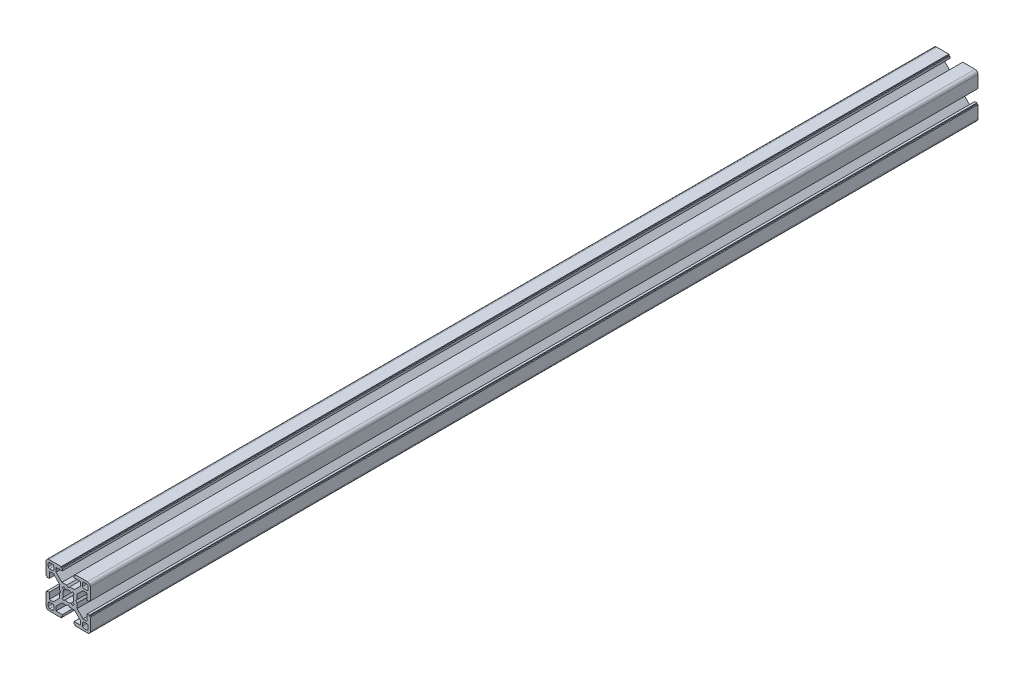
SolidWorks part; units mm, degrees
material "6063-O, Barra estrusa (SS)"
ref_plane "Piano frontale" through (0, 0, 0) normal (0, 0, 1) x (1, 0, 0)
ref_plane "Piano superiore" through (0, 0, 0) normal (0, 1, 0) x (1, 0, 0)
ref_plane "Piano destro" through (0, 0, 0) normal (1, 0, 0) x (0, 0, -1)
sketch "Schizzo1" plane through (0, 0, 0) normal (0, 0, 1) x (1, 0, 0)
  line L0 (-125.0647, 0) -> (53.776, 0) construction
  line L1 (0, -44.8297) -> (0, 95.2781) construction
  line L2 (-15, 13) -> (-15, 4.7)
  line L3 (-15, 4.7) -> (-14.3, 4.7)
  line L4 (-14.3, 4.7) -> (-14.3, 4)
  line L5 (-14.3, 4) -> (-12.8, 4)
  line L6 (-12.8, 4) -> (-12.8, 8.25)
  line L7 (-12.8, 8.25) -> (-10.0178, 8.25)
  line L8 (-10.0178, 8.25) -> (-6, 4.2322)
  line L9 (-6, 4.2322) -> (-6, 1)
  line L10 (-6, 1) -> (-5, 0)
  line L11 (-1, 6) -> (0, 5)
  line L12 (0, 0) -> (-161.3113, 161.3113) construction
  line L13 (-4.2322, 6) -> (-1, 6)
  line L14 (-8.25, 10.0178) -> (-4.2322, 6)
  line L15 (-8.25, 12.8) -> (-8.25, 10.0178)
  line L16 (-4, 12.8) -> (-8.25, 12.8)
  line L17 (-4, 14.3) -> (-4, 12.8)
  line L18 (-4.7, 14.3) -> (-4, 14.3)
  line L19 (-4.7, 15) -> (-4.7, 14.3)
  line L20 (-13, 15) -> (-4.7, 15)
  line L21 (13.5, 10.75) -> (13.5, 12.5)
  line L22 (10.75, 13.5) -> (12.5, 13.5)
  line L23 (9.75, 10.75) -> (9.75, 12.5)
  line L24 (10.75, 9.75) -> (12.5, 9.75)
  line L25 (10.75, -13.5) -> (12.5, -13.5)
  line L26 (13.5, -10.75) -> (13.5, -12.5)
  line L27 (10.75, -9.75) -> (12.5, -9.75)
  line L28 (9.75, -10.75) -> (9.75, -12.5)
  line L29 (-13.5, -10.75) -> (-13.5, -12.5)
  line L30 (-10.75, -13.5) -> (-12.5, -13.5)
  line L31 (-9.75, -10.75) -> (-9.75, -12.5)
  line L32 (-10.75, -9.75) -> (-12.5, -9.75)
  line L33 (1.9955, 3.0562) -> (3.0052, 4.0659)
  line L34 (3.0052, 4.0659) -> (4.0659, 3.0052)
  line L35 (4.0659, 3.0052) -> (3.0562, 1.9955)
  line L36 (3.0562, -1.9955) -> (4.0659, -3.0052)
  line L37 (4.0659, -3.0052) -> (3.0052, -4.0659)
  line L38 (3.0052, -4.0659) -> (1.9955, -3.0562)
  line L39 (-1.9955, -3.0562) -> (-3.0052, -4.0659)
  line L40 (-3.0052, -4.0659) -> (-4.0659, -3.0052)
  line L41 (-4.0659, -3.0052) -> (-3.0562, -1.9955)
  line L42 (1, 6) -> (0, 5)
  line L43 (4.2322, 6) -> (1, 6)
  line L44 (8.25, 10.0178) -> (4.2322, 6)
  line L45 (8.25, 12.8) -> (8.25, 10.0178)
  line L46 (4, 12.8) -> (8.25, 12.8)
  line L47 (12.8, 4) -> (12.8, 8.25)
  line L48 (12.8, 8.25) -> (10.0178, 8.25)
  line L49 (10.0178, 8.25) -> (6, 4.2322)
  line L50 (6, 4.2322) -> (6, 1)
  line L51 (6, 1) -> (5, 0)
  line L52 (6, -1) -> (5, 0)
  line L53 (6, -4.2322) -> (6, -1)
  line L54 (10.0178, -8.25) -> (6, -4.2322)
  line L55 (12.8, -8.25) -> (10.0178, -8.25)
  line L56 (12.8, -4) -> (12.8, -8.25)
  line L57 (4, -12.8) -> (8.25, -12.8)
  line L58 (8.25, -12.8) -> (8.25, -10.0178)
  line L59 (8.25, -10.0178) -> (4.2322, -6)
  line L60 (4.2322, -6) -> (1, -6)
  line L61 (1, -6) -> (0, -5)
  line L62 (-1, -6) -> (0, -5)
  line L63 (-4.2322, -6) -> (-1, -6)
  line L64 (-8.25, -10.0178) -> (-4.2322, -6)
  line L65 (-8.25, -12.8) -> (-8.25, -10.0178)
  line L66 (-4, -12.8) -> (-8.25, -12.8)
  line L67 (-12.8, -4) -> (-12.8, -8.25)
  line L68 (-12.8, -8.25) -> (-10.0178, -8.25)
  line L69 (-10.0178, -8.25) -> (-6, -4.2322)
  line L70 (-6, -4.2322) -> (-6, -1)
  line L71 (-6, -1) -> (-5, 0)
  line L72 (4, 14.3) -> (4, 12.8)
  line L73 (4.7, 14.3) -> (4, 14.3)
  line L74 (4.7, 15) -> (4.7, 14.3)
  line L75 (-3.0562, 1.9955) -> (-4.0659, 3.0052)
  line L76 (-4.0659, 3.0052) -> (-3.0052, 4.0659)
  line L77 (-3.0052, 4.0659) -> (-1.9955, 3.0562)
  line L78 (15, 4.7) -> (14.3, 4.7)
  line L79 (-10.75, 9.75) -> (-12.5, 9.75)
  line L80 (-9.75, 10.75) -> (-9.75, 12.5)
  line L81 (-10.75, 13.5) -> (-12.5, 13.5)
  line L82 (-13.5, 10.75) -> (-13.5, 12.5)
  line L83 (14.3, 4.7) -> (14.3, 4)
  line L84 (14.3, 4) -> (12.8, 4)
  line L85 (14.3, -4) -> (12.8, -4)
  line L86 (14.3, -4.7) -> (14.3, -4)
  line L87 (15, -4.7) -> (14.3, -4.7)
  line L88 (4.7, -15) -> (4.7, -14.3)
  line L89 (4.7, -14.3) -> (4, -14.3)
  line L90 (4, -14.3) -> (4, -12.8)
  line L91 (-4, -14.3) -> (-4, -12.8)
  line L92 (-4.7, -14.3) -> (-4, -14.3)
  line L93 (-4.7, -15) -> (-4.7, -14.3)
  line L94 (-15, -4.7) -> (-14.3, -4.7)
  line L95 (-14.3, -4.7) -> (-14.3, -4)
  line L96 (-14.3, -4) -> (-12.8, -4)
  line L97 (4, 14.3) -> (4, 12.8)
  line L98 (4.7, 14.3) -> (4, 14.3)
  line L99 (4.7, 15) -> (4.7, 14.3)
  line L100 (15, 4.7) -> (14.3, 4.7)
  line L101 (14.3, 4.7) -> (14.3, 4)
  line L102 (14.3, 4) -> (12.8, 4)
  line L103 (13, 15) -> (4.7, 15)
  line L104 (15, 13) -> (15, 4.7)
  line L105 (14.3, -4) -> (12.8, -4)
  line L106 (14.3, -4.7) -> (14.3, -4)
  line L107 (15, -4.7) -> (14.3, -4.7)
  line L108 (4.7, -15) -> (4.7, -14.3)
  line L109 (4.7, -14.3) -> (4, -14.3)
  line L110 (4, -14.3) -> (4, -12.8)
  line L111 (15, -13) -> (15, -4.7)
  line L112 (13, -15) -> (4.7, -15)
  line L113 (-4, -14.3) -> (-4, -12.8)
  line L114 (-4.7, -14.3) -> (-4, -14.3)
  line L115 (-4.7, -15) -> (-4.7, -14.3)
  line L116 (-15, -4.7) -> (-14.3, -4.7)
  line L117 (-14.3, -4.7) -> (-14.3, -4)
  line L118 (-14.3, -4) -> (-12.8, -4)
  line L119 (-13, -15) -> (-4.7, -15)
  line L120 (-15, -13) -> (-15, -4.7)
  arc A0 (-3.65, 0) -> (-3.0562, 1.9955) centre (0, 0) cw
  arc A1 (-1.9955, 3.0562) -> (0, 3.65) centre (0, 0) cw
  arc A2 (-13, 15) -> (-15, 13) centre (-13, 13) ccw
  arc A3 (-13.5, 10.75) -> (-12.5, 9.75) centre (-12.5, 10.75) ccw
  arc A4 (-9.75, 10.75) -> (-10.75, 9.75) centre (-10.75, 10.75) cw
  arc A5 (-10.75, 13.5) -> (-9.75, 12.5) centre (-10.75, 12.5) cw
  arc A6 (-12.5, 13.5) -> (-13.5, 12.5) centre (-12.5, 12.5) ccw
  arc A7 (13.5, 12.5) -> (12.5, 13.5) centre (12.5, 12.5) ccw
  arc A8 (13.5, 10.75) -> (12.5, 9.75) centre (12.5, 10.75) cw
  arc A9 (10.75, 9.75) -> (9.75, 10.75) centre (10.75, 10.75) cw
  arc A10 (10.75, 13.5) -> (9.75, 12.5) centre (10.75, 12.5) ccw
  arc A11 (12.5, -13.5) -> (13.5, -12.5) centre (12.5, -12.5) ccw
  arc A12 (10.75, -13.5) -> (9.75, -12.5) centre (10.75, -12.5) cw
  arc A13 (9.75, -10.75) -> (10.75, -9.75) centre (10.75, -10.75) cw
  arc A14 (13.5, -10.75) -> (12.5, -9.75) centre (12.5, -10.75) ccw
  arc A15 (-13.5, -12.5) -> (-12.5, -13.5) centre (-12.5, -12.5) ccw
  arc A16 (-13.5, -10.75) -> (-12.5, -9.75) centre (-12.5, -10.75) cw
  arc A17 (-10.75, -9.75) -> (-9.75, -10.75) centre (-10.75, -10.75) cw
  arc A18 (-10.75, -13.5) -> (-9.75, -12.5) centre (-10.75, -12.5) ccw
  arc A19 (0, 3.65) -> (1.9955, 3.0562) centre (0, 0) cw
  arc A20 (3.0562, 1.9955) -> (3.65, 0) centre (0, 0) cw
  arc A21 (3.65, 0) -> (3.0562, -1.9955) centre (0, 0) cw
  arc A22 (1.9955, -3.0562) -> (0, -3.65) centre (0, 0) cw
  arc A23 (0, -3.65) -> (-1.9955, -3.0562) centre (0, 0) cw
  arc A24 (-3.0562, -1.9955) -> (-3.65, 0) centre (0, 0) cw
  arc A25 (15, 13) -> (13, 15) centre (13, 13) ccw
  arc A26 (13, -15) -> (15, -13) centre (13, -13) ccw
  arc A27 (-15, -13) -> (-13, -15) centre (-13, -13) ccw
  point P70 (0, 0)
  point P86 (0, 0)
  point P88 (-15, 15)
  point P100 (-9.75, 9.75)
  point P107 (0, 0)
  point P144 (0, 0)
  point P169 (0, 0)
  point P197 (0, 0)
  dimension "D11" = 7.3
  dimension "D14" = 2
  dimension "D17" = 1
  dimension "D1" = 45
  dimension "D2" = 8
  dimension "D3" = 16.5
  dimension "D4" = 9
  dimension "D5" = 2.2
  dimension "D6" = 15
  dimension "D7" = 2.5
  dimension "D8" = 8.3
  dimension "D9" = 2
  dimension "D12" = 5
  dimension "D13" = 1.5
  dimension "D15" = 1.5
  dimension "D16" = 1.5
  dimension "D10" = 4
  dimension "D18" = 4
  dimension "D19" = 4
  dimension "D20" = 4
  dimension "D21" = 4
extrude "Estrusione-Estrusione2" add sketch "Schizzo1" along normal blind 600 contours L120 A27 L119 L93 L92 L91 L66 L65 L64 L63 L62 L61 L60 L59 L58 L57 L90 L89 L88 L112 A26 L111 L87 L86 L85 L56 L55 L54 L53 L52 L51 L50 L49 L48 L47 L84 L83 L78 L104 A25 L103 L74 L73 L72 L46 L45 L44 L43 L42 L11 L13
